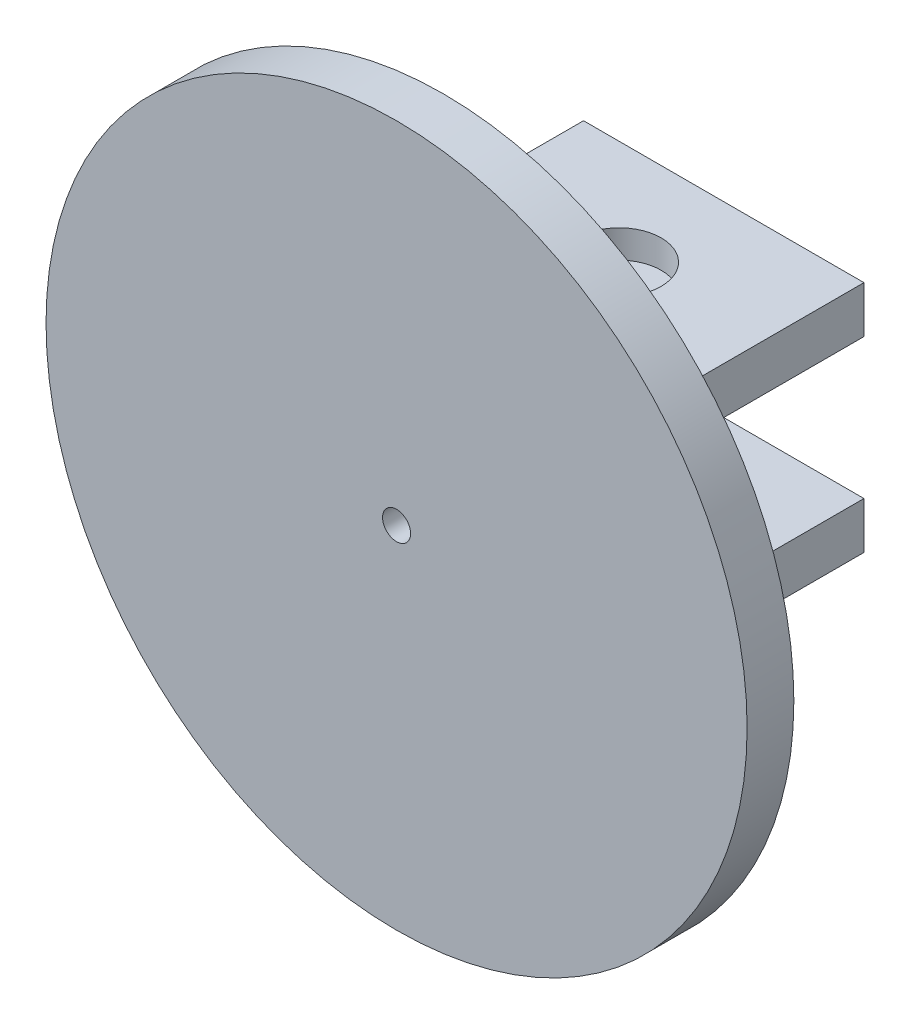
SolidWorks part; units mm, degrees
ref_plane "Front Plane" through (0, 0, 0) normal (0, 0, 1) x (1, 0, 0)
ref_plane "Top Plane" through (0, 0, 0) normal (0, 1, 0) x (1, 0, 0)
ref_plane "Right Plane" through (0, 0, 0) normal (1, 0, 0) x (0, 0, -1)
sketch "Sketch1" plane through (0, 0, 0) normal (0, 0, 1) x (1, 0, 0)
  circle A0 centre (0, 0) radius 75
  dimension "D1" = 150
extrude "Boss-Extrude1" add sketch "Sketch1" along normal blind 10
sketch "Sketch2" plane through (0, 0, 10) normal (0, 0, 1) x (1, 0, 0)
  circle A0 centre (0, 0) radius 3
  dimension "D1" = 6
extrude "Cut-Extrude1" cut sketch "Sketch2" against normal up to next
sketch "Sketch3" plane through (0, 0, 0) normal (0, 0, -1) x (-1, 0, 0)
  line L0 (-58.3098, 0) -> (62.721, 0) construction
  line L1 (-30, 15) -> (30, 15)
  line L2 (-30, 15) -> (-30, 25)
  line L3 (-30, 25) -> (30, 25)
  line L4 (30, 15) -> (30, 25)
  line L5 (30, -15) -> (30, -25)
  line L6 (-30, -25) -> (30, -25)
  line L7 (-30, -15) -> (-30, -25)
  line L8 (-30, -15) -> (30, -15)
  dimension "D1" = 60
  dimension "D2" = 10
  dimension "D3" = 30
  dimension "D4" = 15
extrude "Boss-Extrude2" add sketch "Sketch3" along normal blind 60
sketch "Sketch4" plane through (0, -25, 0) normal (0, -1, 0) x (1, 0, 0)
  line L0 (0, 0) -> (0, -58.7131) construction
  circle A0 centre (0, -37.6) radius 9
  dimension "D1" = 18
  dimension "D2" = 37.6
extrude "Cut-Extrude2" cut sketch "Sketch4" against normal through all
sketch "Sketch6" plane through (0, 15, 0) normal (0, -1, 0) x (1, 0, 0)
  circle A0 centre (0, -37.6) radius 9
  circle A1 centre (0, -37.6) radius 4.5
  dimension "D1" = 9
extrude "Boss-Extrude3" add sketch "Sketch6" against normal blind 4
sketch "Sketch9" plane through (0, -25, 0) normal (0, -1, 0) x (1, 0, 0)
  line L0 (-5, -2.5) -> (5, -2.5) construction
  line L1 (-25.4859, -30) -> (22.9539, -30) construction
  line L3 (0, -37.6) -> (0, -2.5) construction
  line L4 (30, 0) -> (-30, 0) construction
  line L5 (-5, -53) -> (5.2858, -53) construction
  circle A0 centre (-5, -2.5) radius 2.25
  circle A1 centre (5, -2.5) radius 2.25
  circle A2 centre (-5, -53) radius 2.25
  circle A3 centre (5.2858, -53) radius 2.25
  dimension "D1" = 4.5
  dimension "D5" = 4.5
  dimension "D2" = 10
  dimension "D3" = 35.1
  dimension "D4" = 30
  dimension "D6" = 15.4
extrude "Cut-Extrude5" cut sketch "Sketch9" against normal blind 10
mirror "Mirror1" about plane through (0, 0, 0) normal (0, 1, 0) of "Boss-Extrude3"
